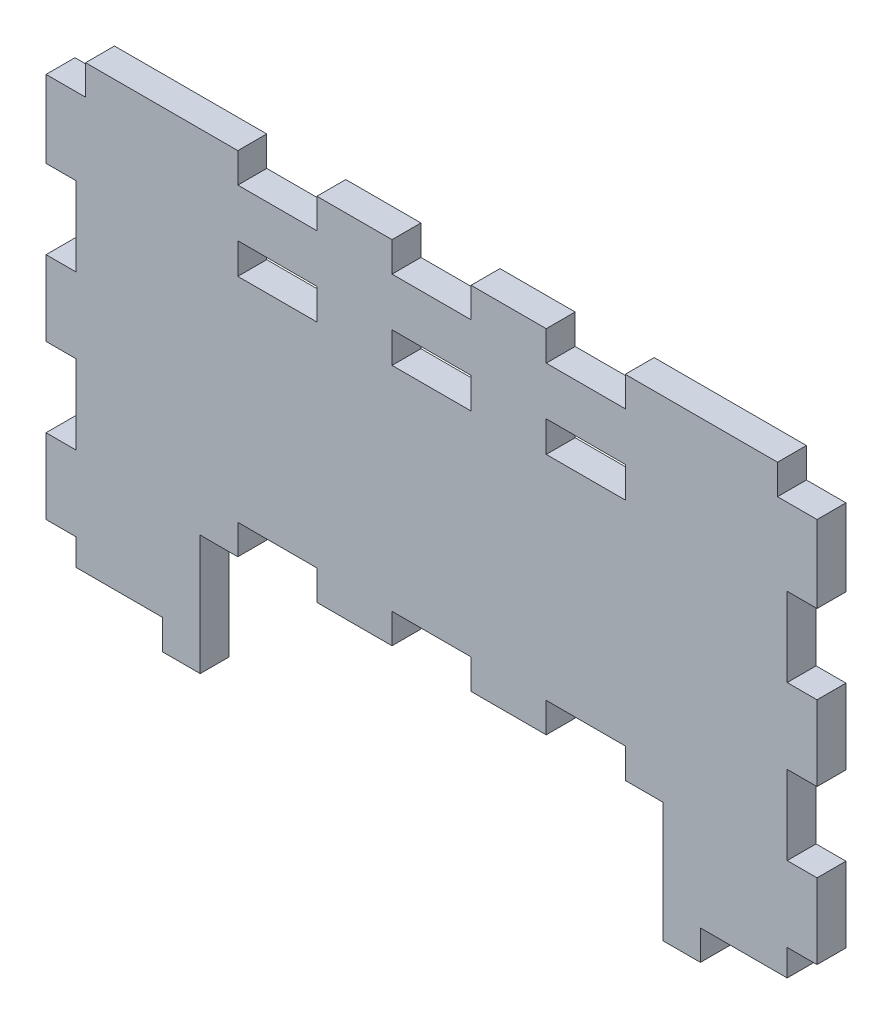
SolidWorks part; units mm, degrees
ref_plane "Front Plane" through (0, 0, 0) normal (0, 0, 1) x (1, 0, 0)
ref_plane "Top Plane" through (0, 0, 0) normal (0, 1, 0) x (1, 0, 0)
ref_plane "Right Plane" through (0, 0, 0) normal (1, 0, 0) x (0, 0, -1)
sketch "Sketch1" plane through (0, 0, 0) normal (0, 0, 1) x (1, 0, 0)
  line L0 (80, 3.175) -> (0, 3.175) construction
  line L1 (0, 52.125) -> (80, 52.125)
  line L2 (0, 52.125) -> (0, 3.175)
  line L3 (0, 3.175) -> (80, 3.175) construction
  line L4 (80, 52.125) -> (80, 3.175)
  line L5 (80, 52.125) -> (0, 52.125) construction
  line L6 (0, 52.125) -> (0, 3.175) construction
  line L7 (80, 52.125) -> (80, 3.175) construction
  line L8 (3, 49.125) -> (77, 49.125) construction
  line L9 (77, 49.125) -> (77, 6.175) construction
  line L10 (3, 6.175) -> (77, 6.175) construction
  line L11 (3, 49.125) -> (3, 6.175) construction
  line L12 (77, 49.125) -> (3, 49.125) construction
  line L13 (0, 18.625) -> (80, 18.625) construction
  line L14 (0, 15.625) -> (80, 15.625) construction
  line L15 (0, 40.925) -> (80, 40.925) construction
  line L16 (0, 37.925) -> (80, 37.925) construction
  line L17 (0, 37.925) -> (80, 37.925) construction
  line L18 (0, 40.925) -> (80, 40.925) construction
  line L19 (0, 15.625) -> (80, 15.625) construction
  line L20 (80, 18.625) -> (0, 18.625) construction
  line L21 (16, 3.175) -> (16, 15.625)
  line L22 (16, 15.625) -> (64, 15.625)
  line L23 (64, 15.625) -> (64, 3.175)
  line L24 (16, 3.175) -> (16, 15.625) construction
  line L25 (64, 15.625) -> (64, 3.175) construction
  line L26 (16, 3.175) -> (0, 3.175)
  line L27 (64, 3.175) -> (80, 3.175)
  circle A0 centre (37.4, 29.175) radius 21 construction
  circle A1 centre (37.4, 29.175) radius 24 construction
  circle A2 centre (37.4, 29.175) radius 24 construction
  circle A3 centre (37.4, 29.175) radius 21 construction
sketch "Sketch2" plane through (0, 0, 0) normal (1, 0, 0) x (0, 0, -1)
  line L1 (0, 52.125) -> (3, 52.125)
  line L2 (0, 52.125) -> (0, 3.175)
  line L3 (0, 3.175) -> (3, 3.175)
  line L4 (3, 52.125) -> (3, 3.175)
extrude "Boss-Extrude1" add sketch "Sketch1" against normal up to vertex (3 mm away) up to point (0, 52.125, -3)
sketch "Sketch3" plane through (0, 0, 0) normal (0, 0, 1) x (1, 0, 0)
  line L4 (4.1, 52.225) -> (-0.1, 52.225)
  line L5 (-0.1, 52.225) -> (-0.1, 49.025)
  line L6 (-0.1, 49.025) -> (4.1, 49.025)
  line L7 (4.1, 49.025) -> (4.1, 52.225)
  line L8 (4, 52.125) -> (0, 52.125)
  line L9 (0, 52.125) -> (0, 49.125)
  line L10 (0, 49.125) -> (4, 49.125)
  line L11 (4, 49.125) -> (4, 52.125)
  line L12 (4, 52.125) -> (0, 52.125) construction
  line L13 (0, 52.125) -> (0, 49.125) construction
  line L14 (0, 49.125) -> (4, 49.125) construction
  line L15 (4, 49.125) -> (4, 52.125) construction
  line L16 (3, 16.925) -> (3, 24.925)
  line L17 (3, 24.925) -> (0, 24.925)
  line L18 (0, 24.925) -> (0, 16.925)
  line L19 (0, 16.925) -> (3, 16.925)
  line L20 (3, 16.925) -> (3, 24.925) construction
  line L21 (3, 24.925) -> (0, 24.925) construction
  line L22 (0, 24.925) -> (0, 16.925) construction
  line L23 (0, 16.925) -> (3, 16.925) construction
  line L24 (28, 18.625) -> (20, 18.625)
  line L25 (20, 18.625) -> (20, 15.625)
  line L26 (20, 15.625) -> (28, 15.625)
  line L27 (28, 15.625) -> (28, 18.625)
  line L28 (28, 18.625) -> (20, 18.625) construction
  line L29 (20, 18.625) -> (20, 15.625) construction
  line L30 (20, 15.625) -> (28, 15.625) construction
  line L31 (28, 15.625) -> (28, 18.625) construction
  line L32 (44, 18.625) -> (36, 18.625)
  line L33 (44, 15.625) -> (44, 18.625)
  line L34 (36, 15.625) -> (44, 15.625)
  line L35 (36, 18.625) -> (36, 15.625)
  line L36 (44, 18.625) -> (36, 18.625) construction
  line L37 (44, 15.625) -> (44, 18.625) construction
  line L38 (36, 15.625) -> (44, 15.625) construction
  line L39 (36, 18.625) -> (36, 15.625) construction
  line L40 (3, 32.925) -> (3, 40.925)
  line L41 (0, 32.925) -> (3, 32.925)
  line L42 (0, 40.925) -> (0, 32.925)
  line L43 (3, 40.925) -> (0, 40.925)
  line L44 (3, 32.925) -> (3, 40.925) construction
  line L45 (0, 32.925) -> (3, 32.925) construction
  line L46 (0, 40.925) -> (0, 32.925) construction
  line L47 (3, 40.925) -> (0, 40.925) construction
  line L48 (36, 49.125) -> (44, 49.125)
  line L49 (44, 49.125) -> (44, 52.125)
  line L50 (44, 52.125) -> (36, 52.125)
  line L51 (36, 52.125) -> (36, 49.125)
  line L52 (36, 49.125) -> (44, 49.125) construction
  line L53 (44, 49.125) -> (44, 52.125) construction
  line L54 (44, 52.125) -> (36, 52.125) construction
  line L55 (36, 52.125) -> (36, 49.125) construction
  line L56 (44, 43.925) -> (36, 43.925)
  line L57 (44, 40.925) -> (44, 43.925)
  line L58 (36, 40.925) -> (44, 40.925)
  line L59 (36, 43.925) -> (36, 40.925)
  line L60 (44, 43.925) -> (36, 43.925) construction
  line L61 (44, 40.925) -> (44, 43.925) construction
  line L62 (36, 40.925) -> (44, 40.925) construction
  line L63 (36, 43.925) -> (36, 40.925) construction
  line L64 (28, 43.925) -> (20, 43.925)
  line L65 (28, 40.925) -> (28, 43.925)
  line L66 (20, 40.925) -> (28, 40.925)
  line L67 (20, 43.925) -> (20, 40.925)
  line L68 (28, 43.925) -> (20, 43.925) construction
  line L69 (28, 40.925) -> (28, 43.925) construction
  line L70 (20, 40.925) -> (28, 40.925) construction
  line L71 (20, 43.925) -> (20, 40.925) construction
  line L72 (20, 49.125) -> (28, 49.125)
  line L73 (28, 49.125) -> (28, 52.125)
  line L74 (28, 52.125) -> (20, 52.125)
  line L78 (20, 52.125) -> (20, 49.125)
  line L79 (20, 49.125) -> (28, 49.125) construction
  line L80 (28, 49.125) -> (28, 52.125) construction
  line L82 (28, 52.125) -> (20, 52.125) construction
  line L83 (20, 52.125) -> (20, 49.125) construction
  line L84 (60, 40.925) -> (60, 43.925)
  line L85 (52, 40.925) -> (60, 40.925)
  line L86 (52, 43.925) -> (52, 40.925)
  line L87 (60, 43.925) -> (52, 43.925)
  line L88 (60, 40.925) -> (60, 43.925) construction
  line L89 (52, 40.925) -> (60, 40.925) construction
  line L90 (52, 43.925) -> (52, 40.925) construction
  line L91 (60, 43.925) -> (52, 43.925) construction
  line L92 (52, 18.625) -> (52, 15.625)
  line L93 (52, 15.625) -> (60, 15.625)
  line L94 (60, 15.625) -> (60, 18.625)
  line L95 (60, 18.625) -> (52, 18.625)
  line L96 (52, 18.625) -> (52, 15.625) construction
  line L97 (52, 15.625) -> (60, 15.625) construction
  line L98 (60, 15.625) -> (60, 18.625) construction
  line L99 (60, 18.625) -> (52, 18.625) construction
  line L100 (77, 40.925) -> (77, 32.925)
  line L101 (77, 32.925) -> (80, 32.925)
  line L102 (80, 32.925) -> (80, 40.925)
  line L106 (80, 40.925) -> (77, 40.925)
  line L107 (77, 40.925) -> (77, 32.925) construction
  line L108 (77, 32.925) -> (80, 32.925) construction
  line L110 (80, 32.925) -> (80, 40.925) construction
  line L111 (80, 40.925) -> (77, 40.925) construction
  line L112 (76, 52.125) -> (76, 49.125)
  line L113 (76, 49.125) -> (80, 49.125)
  line L114 (80, 49.125) -> (80, 52.125)
  line L115 (80, 52.125) -> (76, 52.125)
  line L116 (76, 52.125) -> (76, 49.125) construction
  line L117 (76, 49.125) -> (80, 49.125) construction
  line L118 (80, 49.125) -> (80, 52.125) construction
  line L119 (80, 52.125) -> (76, 52.125) construction
  line L120 (77, 24.925) -> (77, 16.925)
  line L121 (80, 24.925) -> (77, 24.925)
  line L122 (80, 16.925) -> (80, 24.925)
  line L123 (77, 16.925) -> (80, 16.925)
  line L124 (77, 24.925) -> (77, 16.925) construction
  line L125 (80, 24.925) -> (77, 24.925) construction
  line L126 (80, 16.925) -> (80, 24.925) construction
  line L127 (77, 16.925) -> (80, 16.925) construction
  line L128 (60, 49.125) -> (60, 52.125)
  line L129 (52, 49.125) -> (60, 49.125)
  line L130 (52, 52.125) -> (52, 49.125)
  line L131 (60, 52.125) -> (52, 52.125)
  line L134 (60, 49.125) -> (60, 52.125) construction
  line L135 (52, 49.125) -> (60, 49.125) construction
  line L136 (52, 52.125) -> (52, 49.125) construction
  line L137 (60, 52.125) -> (52, 52.125) construction
  line L138 (3.1, 16.825) -> (3.1, 25.025)
  line L139 (3.1, 25.025) -> (-0.1, 25.025)
  line L140 (77, 8.925) -> (77, 6.175)
  line L141 (77, 6.175) -> (68, 6.175)
  line L142 (68, 6.175) -> (68, 3.175)
  line L143 (68, 3.175) -> (80, 3.175)
  line L144 (80, 3.175) -> (80, 8.925)
  line L145 (80, 8.925) -> (77, 8.925)
  line L146 (77, 8.925) -> (77, 6.175) construction
  line L147 (77, 6.175) -> (68, 6.175) construction
  line L148 (68, 6.175) -> (68, 3.175) construction
  line L149 (68, 3.175) -> (80, 3.175) construction
  line L150 (80, 3.175) -> (80, 8.925) construction
  line L151 (80, 8.925) -> (77, 8.925) construction
  line L152 (3, 6.175) -> (3, 8.925)
  line L153 (3, 8.925) -> (0, 8.925)
  line L154 (0, 8.925) -> (0, 3.175)
  line L155 (0, 3.175) -> (12, 3.175)
  line L156 (12, 3.175) -> (12, 6.175)
  line L157 (12, 6.175) -> (3, 6.175)
  line L304 (3, 6.175) -> (3, 8.925) construction
  line L305 (3, 8.925) -> (0, 8.925) construction
  line L306 (0, 8.925) -> (0, 3.175) construction
  line L307 (0, 3.175) -> (12, 3.175) construction
  line L308 (12, 3.175) -> (12, 6.175) construction
  line L309 (12, 6.175) -> (3, 6.175) construction
  line L310 (-0.1, 25.025) -> (-0.1, 16.825)
  line L311 (-0.1, 16.825) -> (3.1, 16.825)
  line L312 (28.1, 18.725) -> (19.9, 18.725)
  line L313 (19.9, 18.725) -> (19.9, 15.525)
  line L314 (19.9, 15.525) -> (28.1, 15.525)
  line L315 (28.1, 15.525) -> (28.1, 18.725)
  line L316 (44.1, 18.725) -> (35.9, 18.725)
  line L317 (35.9, 18.725) -> (35.9, 15.525)
  line L318 (35.9, 15.525) -> (44.1, 15.525)
  line L319 (44.1, 15.525) -> (44.1, 18.725)
  line L320 (3.1, 32.825) -> (3.1, 41.025)
  line L321 (3.1, 41.025) -> (-0.1, 41.025)
  line L322 (-0.1, 41.025) -> (-0.1, 32.825)
  line L323 (-0.1, 32.825) -> (3.1, 32.825)
  line L324 (35.9, 49.025) -> (44.1, 49.025)
  line L325 (44.1, 49.025) -> (44.1, 52.225)
  line L326 (44.1, 52.225) -> (35.9, 52.225)
  line L327 (35.9, 52.225) -> (35.9, 49.025)
  line L328 (44.1, 44.025) -> (35.9, 44.025)
  line L329 (35.9, 44.025) -> (35.9, 40.825)
  line L330 (35.9, 40.825) -> (44.1, 40.825)
  line L331 (44.1, 40.825) -> (44.1, 44.025)
  line L332 (28.1, 44.025) -> (19.9, 44.025)
  line L333 (19.9, 44.025) -> (19.9, 40.825)
  line L334 (19.9, 40.825) -> (28.1, 40.825)
  line L335 (28.1, 40.825) -> (28.1, 44.025)
  line L336 (19.9, 49.025) -> (28.1, 49.025)
  line L337 (28.1, 49.025) -> (28.1, 52.225)
  line L338 (28.1, 52.225) -> (19.9, 52.225)
  line L339 (19.9, 52.225) -> (19.9, 49.025)
  line L340 (60.1, 40.825) -> (60.1, 44.025)
  line L341 (60.1, 44.025) -> (51.9, 44.025)
  line L342 (51.9, 44.025) -> (51.9, 40.825)
  line L343 (51.9, 40.825) -> (60.1, 40.825)
  line L344 (51.9, 18.725) -> (51.9, 15.525)
  line L345 (51.9, 15.525) -> (60.1, 15.525)
  line L346 (60.1, 15.525) -> (60.1, 18.725)
  line L347 (60.1, 18.725) -> (51.9, 18.725)
  line L348 (76.9, 41.025) -> (76.9, 32.825)
  line L349 (76.9, 32.825) -> (80.1, 32.825)
  line L350 (80.1, 32.825) -> (80.1, 41.025)
  line L351 (80.1, 41.025) -> (76.9, 41.025)
  line L352 (75.9, 52.225) -> (75.9, 49.025)
  line L353 (75.9, 49.025) -> (80.1, 49.025)
  line L354 (80.1, 49.025) -> (80.1, 52.225)
  line L355 (80.1, 52.225) -> (75.9, 52.225)
  line L356 (76.9, 25.025) -> (76.9, 16.825)
  line L357 (76.9, 16.825) -> (80.1, 16.825)
  line L358 (80.1, 16.825) -> (80.1, 25.025)
  line L359 (80.1, 25.025) -> (76.9, 25.025)
  line L360 (60.1, 49.025) -> (60.1, 52.225)
  line L361 (60.1, 52.225) -> (51.9, 52.225)
  line L362 (51.9, 52.225) -> (51.9, 49.025)
  line L363 (51.9, 49.025) -> (60.1, 49.025)
  line L364 (76.9, 9.025) -> (76.9, 6.275)
  line L365 (76.9, 6.275) -> (67.9, 6.275)
  line L366 (67.9, 6.275) -> (67.9, 3.075)
  line L367 (67.9, 3.075) -> (80.1, 3.075)
  line L368 (80.1, 3.075) -> (80.1, 9.025)
  line L369 (80.1, 9.025) -> (76.9, 9.025)
  line L370 (3.1, 6.275) -> (3.1, 9.025)
  line L371 (3.1, 9.025) -> (-0.1, 9.025)
  line L372 (-0.1, 9.025) -> (-0.1, 3.075)
  line L373 (-0.1, 3.075) -> (12.1, 3.075)
  line L374 (12.1, 3.075) -> (12.1, 6.275)
  line L375 (12.1, 6.275) -> (3.1, 6.275)
  dimension "D1" = 0
  dimension "D2" = 0
  dimension "D3" = 0
  dimension "D4" = 0
  dimension "D5" = 0
  dimension "D6" = 0
  dimension "D7" = 0
  dimension "D8" = 0
  dimension "D9" = 0
  dimension "D10" = 0
  dimension "D11" = 0
  dimension "D12" = 0
  dimension "D13" = 0
  dimension "D14" = 0
  dimension "D15" = 0
  dimension "D16" = 0
  dimension "D17" = 0
  dimension "D18" = 0.1
extrude "Cut-Extrude1" cut sketch "Sketch3" against normal through all
